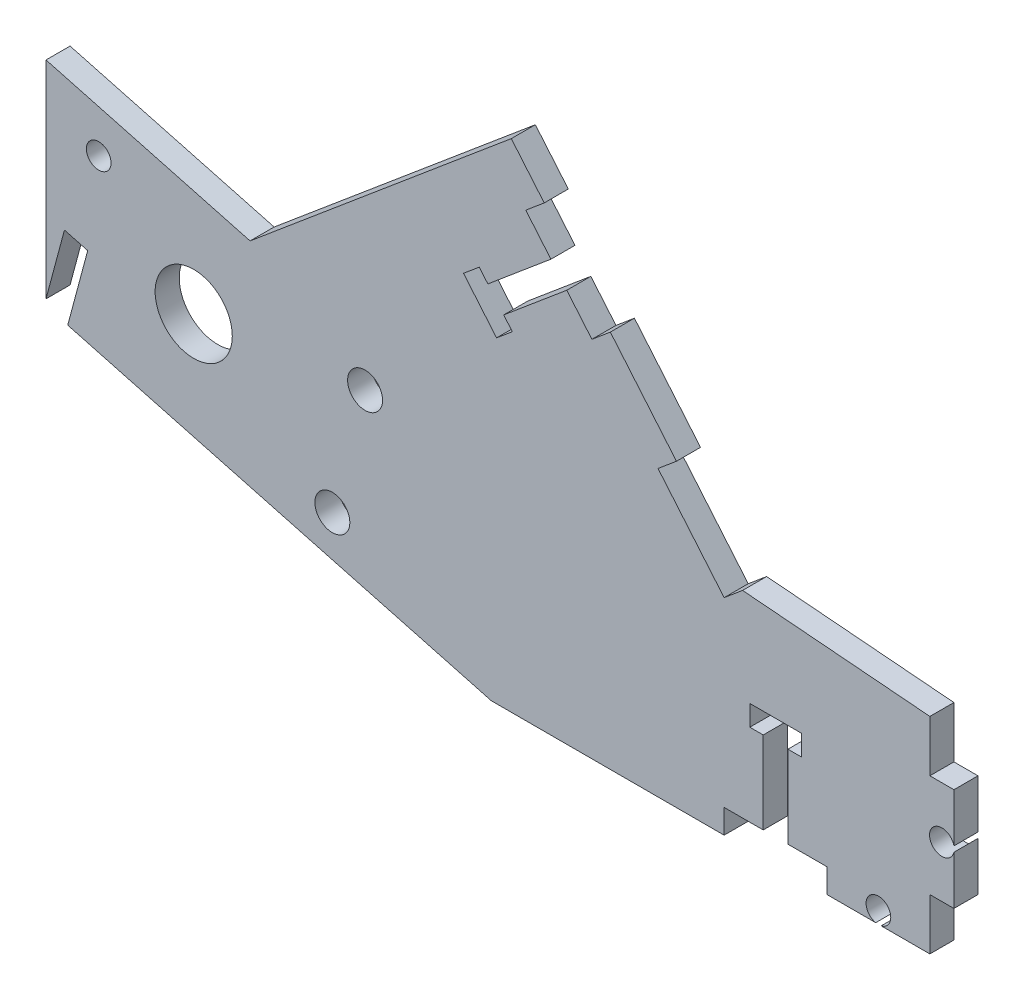
SolidWorks part; units mm, degrees
ref_plane "Front Plane" through (0, 0, 0) normal (0, 0, 1) x (1, 0, 0)
ref_plane "Top Plane" through (0, 0, 0) normal (0, 1, 0) x (1, 0, 0)
ref_plane "Right Plane" through (0, 0, 0) normal (1, 0, 0) x (0, 0, -1)
sketch "Sketch1" plane through (0, 0, 0) normal (0, 0, 1) x (1, 0, 0)
  line L0 (-99.869, 38.548) -> (-50.8, 25.4)
  line L1 (-99.869, 38.548) -> (-106.443, 14.0135)
  line L3 (-106.443, 14.0135) -> (-54.144, 0)
  line L4 (-54.144, 0) -> (0, 0)
  line L5 (0, 0) -> (0, 25.4)
  line L6 (0, 25.4) -> (-50.8, 25.4)
  line L7 (-103.156, 26.2807) -> (-90.8888, 22.9937) construction
  line L8 (-90.8888, 22.9937) -> (-88.8673, 30.5381) construction
  line L9 (-88.8673, 30.5381) -> (-69.7303, 25.4104) construction
  line L10 (-90.8888, 22.9937) -> (-92.9103, 15.4494) construction
  line L11 (-92.9103, 15.4494) -> (-73.7734, 10.3217) construction
  line L12 (-25.4, 25.4) -> (-33.5634, 35.1288)
  line L13 (-25.4, 0) -> (-12.7, 0)
  line L14 (-25.4, 0) -> (-25.4, 2.9718)
  line L15 (-25.4, 2.9718) -> (-12.7, 2.9718)
  line L16 (-12.7, 0) -> (-12.7, 2.9718)
  line L17 (-25.4, 25.4) -> (-23.1235, 27.3102)
  line L18 (-33.5634, 35.1288) -> (-31.2869, 37.039)
  line L19 (-23.1235, 27.3102) -> (-31.2869, 37.039)
  line L20 (-103.9778, 23.2139) -> (-102.3343, 29.3476)
  line L21 (-103.9778, 23.2139) -> (-106.8483, 23.9831)
  line L22 (-102.3343, 29.3476) -> (-105.2048, 30.1167)
  line L23 (-106.8483, 23.9831) -> (-105.2048, 30.1167)
  line L24 (-103.156, 26.2807) -> (-106.0266, 27.0499) construction
  line L25 (-106.8483, 23.9831) -> (-109.1263, 15.4815)
  line L26 (0, 19.05) -> (2.9718, 19.05)
  line L27 (0, 19.05) -> (0, 6.35)
  line L28 (0, 6.35) -> (2.9718, 6.35)
  line L29 (2.9718, 19.05) -> (2.9718, 6.35)
  line L30 (-109.1263, 15.4815) -> (-109.1263, 41.0285)
  line L31 (-51.6788, 61.3411) -> (-83.9318, 34.2776)
  line L32 (-51.6788, 61.3411) -> (-21.5206, 25.4)
  line L33 (-47.6137, 56.4965) -> (-39.4503, 46.7678)
  line L34 (-47.6137, 56.4965) -> (-49.8902, 54.5863)
  line L35 (-39.4503, 46.7678) -> (-41.7268, 44.8575)
  line L36 (-49.8902, 54.5863) -> (-41.7268, 44.8575)
  line L37 (-109.1263, 41.0285) -> (-99.869, 38.548)
  line L38 (0, 25.4) -> (-23.1235, 27.3102)
  circle A0 centre (-90.8888, 22.9937) radius 4.7625
  circle A1 centre (-69.7303, 25.4104) radius 2.159
  circle A2 centre (-73.7734, 10.3217) radius 2.159
  dimension "D5" = 9.525
  dimension "D10" = 4.318
  dimension "D1" = 25.4
  dimension "D2" = 50.8
  dimension "D3" = 50.8
  dimension "D4" = 165
  dimension "D6" = 25.4
  dimension "D7" = 12.7
  dimension "D8" = 7.8105
  dimension "D9" = 19.812
  dimension "D11" = 12.7
  dimension "D12" = 2.9718
  dimension "D13" = 12.7
  dimension "D14" = 12.7
  dimension "D15" = 2.9718
  dimension "D16" = 50
  dimension "D17" = 25.4
  dimension "D18" = 25.4
  dimension "D19" = 2.9718
  dimension "D20" = 6.35
  dimension "D21" = 2.9718
  dimension "D22" = 12.7
  dimension "D23" = 6.35
  dimension "D24" = 31.7242
  dimension "D25" = 6.3242
  dimension "D26" = 2.9718
  dimension "D27" = 12.7
extrude "Boss-Extrude1" add sketch "Sketch1" along normal blind 2.9718
sketch "Sketch2" plane through (0, 0, 2.9718) normal (0, 0, 1) x (1, 0, 0)
  line L0 (0, 19.05) -> (2.9718, 19.05) construction
  line L1 (2.9718, 19.05) -> (2.9718, 6.35) construction
  line L2 (-12.7, 1.4859) -> (0, 1.4859) construction
  line L3 (-12.7, 0) -> (-12.7, 2.9718) construction
  line L4 (0, 0) -> (0, 6.35) construction
  line L5 (-6.35, 0) -> (-6.35, 1.4859) construction
  line L6 (-12.7, 0) -> (0, 0) construction
  line L7 (-105.4131, 23.5985) -> (-101.3043, 38.9326) construction
  line L10 (-103.9778, 23.2139) -> (-106.8483, 23.9831) construction
  line L14 (-19.05, 2.9718) -> (-19.05, 15.6718) construction
  line L15 (-25.4, 2.9718) -> (-12.7, 2.9718) construction
  line L16 (-22.225, 15.6718) -> (-15.875, 15.6718)
  line L17 (-106.8483, 40.4181) -> (-71.0258, 30.8195) construction
  line L20 (-45.8085, 49.7219) -> (-55.5373, 41.5585) construction
  line L21 (-49.8902, 54.5863) -> (-41.7268, 44.8575) construction
  line L22 (-57.5781, 43.9907) -> (-53.4964, 39.1263)
  line L23 (-46.7881, 50.8894) -> (-54.5711, 44.3586)
  line L25 (-17.526, 2.9718) -> (-17.526, 13.1318)
  line L27 (-44.8289, 48.5545) -> (-52.6119, 42.0237)
  line L29 (-20.574, 2.9718) -> (-20.574, 13.1318)
  line L31 (-55.6324, 45.6234) -> (-54.5711, 44.3586)
  line L34 (-22.225, 13.1318) -> (-20.574, 13.1318)
  line L35 (-55.6324, 45.6234) -> (-57.5781, 43.9907)
  line L37 (-53.4964, 39.1263) -> (-51.5507, 40.759)
  line L40 (-15.875, 15.6718) -> (-15.875, 13.1318)
  line L41 (-22.225, 15.6718) -> (-22.225, 13.1318)
  line L46 (-52.6119, 42.0237) -> (-51.5507, 40.759)
  line L49 (-17.526, 13.1318) -> (-15.875, 13.1318)
  line L50 (-55.6324, 45.6234) -> (-51.5507, 40.759) construction
  line L51 (-46.7881, 50.8894) -> (-56.5169, 42.726) construction
  line L52 (-44.8289, 48.5545) -> (-54.5577, 40.3911) construction
  line L54 (-22.225, 13.1318) -> (-15.875, 13.1318) construction
  line L55 (-20.574, 2.9718) -> (-20.574, 15.6718) construction
  line L56 (-17.526, 2.9718) -> (-17.526, 15.6718) construction
  line L57 (-46.7881, 50.8894) -> (-44.8289, 48.5545)
  line L61 (-17.526, 2.9718) -> (-20.574, 2.9718)
  circle A0 centre (1.4859, 12.7) radius 1.524
  circle A1 centre (-6.35, 1.4859) radius 1.524
  circle A2 centre (-102.6191, 34.0257) radius 1.524
  point P4 (1.4859, 19.05)
  point P8 (2.9718, 12.7)
  point P19 (0, 0)
  point P41 (-19.05, 15.6718)
  point P55 (-55.5373, 41.5585)
  point P57 (0, 22.479)
  point P58 (-12.7, 22.479)
  point P61 (-105.687, 16.835)
  point P62 (-93.4198, 13.548)
  point P65 (0, 19.431)
  point P66 (-12.7, 19.431)
  point P69 (-104.8981, 19.7791)
  point P70 (-92.6309, 16.4921)
  point P73 (-96.3005, 12.6106)
  point P74 (-94.657, 18.7442)
  point P75 (-10.16, 17.78)
  point P76 (-10.16, 24.13)
  dimension "D1" = 5.08
  dimension "D4" = 1.524
  dimension "D5" = 1.524
  dimension "D6" = 2.54
extrude "Cut-Extrude2" cut sketch "Sketch2" against normal through all contours L27 L46 L37 L22 L35 L31 L23 L57 | A2 | L40 L49 L25 L61 L29 L34 L41 L16 | A0 | A1
